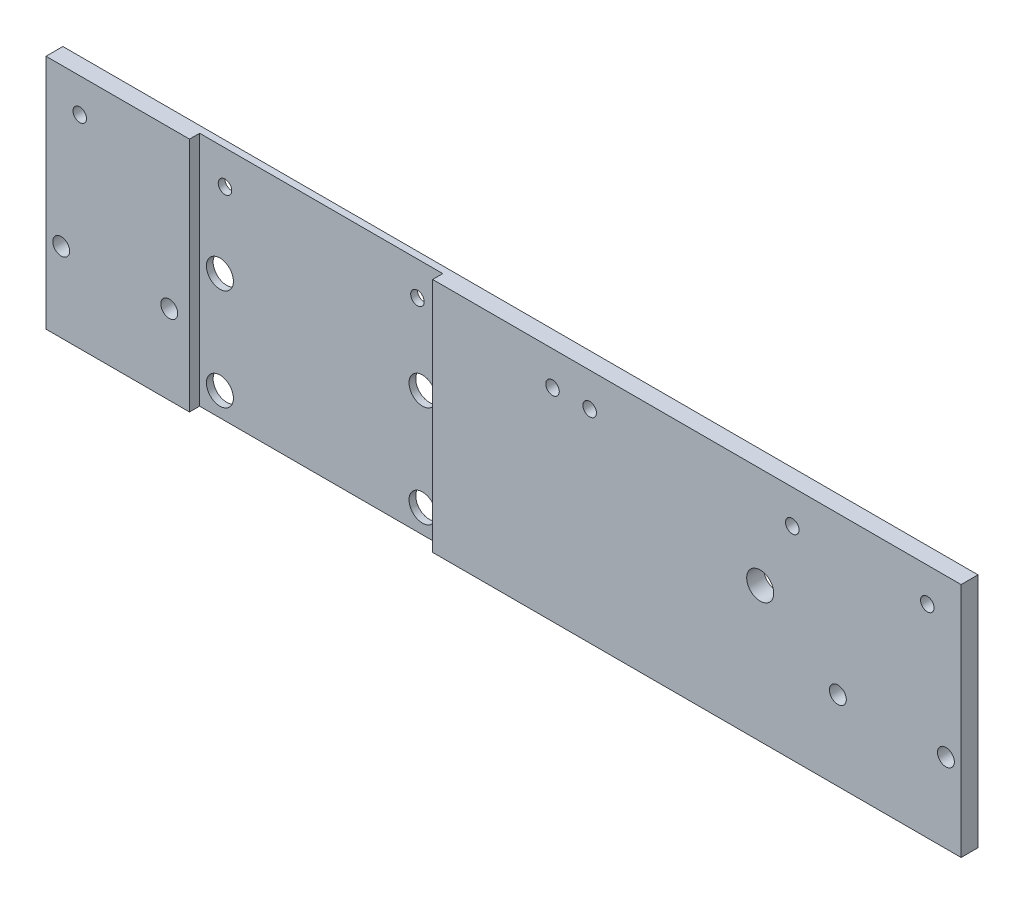
SolidWorks part; units mm, degrees
ref_plane "Ebene vorne" through (0, 0, 0) normal (0, 0, 1) x (1, 0, 0)
ref_plane "Ebene oben" through (0, 0, 0) normal (0, 1, 0) x (1, 0, 0)
ref_plane "Ebene rechts" through (0, 0, 0) normal (1, 0, 0) x (0, 0, -1)
sketch "Skizze1" plane through (0, 0, 0) normal (0, 0, 1) x (1, 0, 0)
  line L1 (0, 0) -> (271, 0)
  line L2 (0, 0) -> (0, 70)
  line L3 (0, 70) -> (271, 70)
  line L4 (271, 0) -> (271, 70)
  dimension "D1" = 271
  dimension "D2" = 70
extrude "Aufsatz-Linear austragen1" add sketch "Skizze1" along normal blind 5
sketch "Skizze2" plane through (0, 0, 5) normal (0, 0, 1) x (1, 0, 0)
  line L0 (271, 70) -> (0, 70) construction
  line L1 (42.5, 70) -> (114.5, 70)
  line L2 (42.5, 70) -> (42.5, 0)
  line L3 (42.5, 0) -> (114.5, 0)
  line L4 (114.5, 70) -> (114.5, 0)
  line L5 (0, 0) -> (271, 0) construction
  line L6 (0, 70) -> (0, 0) construction
  dimension "D1" = 72
  dimension "D2" = 42.5
extrude "Schnitt-Linear austragen1" cut sketch "Skizze2" against normal blind 3
sketch "Skizze3" plane through (0, 0, 0) normal (0, 0, -1) x (-1, 0, 0)
  line L1 (0, 70) -> (0, 0) construction
  line L3 (0, 0) -> (-271, 0) construction
  circle A0 centre (-48.5, 37) radius 4
  circle A1 centre (-108.5, 37) radius 4
  circle A2 centre (-108.5, 7) radius 4
  circle A3 centre (-48.5, 7) radius 4
  dimension "D1" = 8
  dimension "D2" = 30
  dimension "D3" = 48.5
  dimension "D4" = 60
  dimension "D5" = 7
extrude "Schnitt-Linear austragen2" cut sketch "Skizze3" against normal blind 10
sketch "Skizze4" plane through (0, 0, 0) normal (0, 0, -1) x (-1, 0, 0)
  line L3 (-271, 0) -> (-271, 70) construction
  line L4 (0, 0) -> (-271, 0) construction
  circle A0 centre (-234.5, 23.5) radius 2.5
  circle A1 centre (-266.5, 23.5) radius 2.5
  dimension "D1" = 5
  dimension "D2" = 4.5
  dimension "D3" = 23.5
  dimension "D4" = 32
extrude "Schnitt-Linear austragen3" cut sketch "Skizze4" against normal blind 10
sketch "Skizze5" plane through (0, 0, 0) normal (0, 0, -1) x (-1, 0, 0)
  line L0 (0, 0) -> (-271, 0) construction
  line L1 (0, 70) -> (0, 0) construction
  circle A0 centre (-36.5, 23.5) radius 2.5
  circle A1 centre (-4.5, 23.5) radius 2.5
  dimension "D4" = 5
  dimension "D1" = 23.5
  dimension "D2" = 4.5
  dimension "D3" = 32
extrude "Schnitt-Linear austragen4" cut sketch "Skizze5" against normal blind 10
sketch "Skizze6" plane through (0, 0, 0) normal (0, 0, -1) x (-1, 0, 0)
  line L0 (0, 70) -> (0, 0) construction
  line L1 (-114.5, 0) -> (-114.5, 70) construction
  line L2 (-271, 70) -> (0, 70) construction
  line L3 (-271, 0) -> (-271, 70) construction
  circle A0 centre (-10, 60) radius 2
  circle A1 centre (-50, 60) radius 2
  circle A2 centre (-161, 60) radius 2
  circle A3 centre (-221, 60) radius 2
  circle A4 centre (-261, 60) radius 2
  circle A5 centre (-107, 60) radius 2
  dimension "D1" = 4
  dimension "D2" = 10
  dimension "D3" = 10
  dimension "D4" = 50
  dimension "D5" = 10
  dimension "D6" = 50
  dimension "D7" = 110
  dimension "D8" = 7.5
extrude "Schnitt-Linear austragen5" cut sketch "Skizze6" against normal blind 10
sketch "Skizze7" plane through (0, 0, 0) normal (0, 0, -1) x (-1, 0, 0)
  line L0 (-271, 70) -> (0, 70) construction
  line L1 (-271, 0) -> (-271, 70) construction
  circle A0 centre (-211.5, 40) radius 4
  dimension "D3" = 8
  dimension "D1" = 30
  dimension "D2" = 59.5
extrude "Schnitt-Linear austragen6" cut sketch "Skizze7" against normal blind 10
sketch "Skizze8" plane through (0, 0, 0) normal (0, 0, -1) x (-1, 0, 0)
  line L0 (-271, 70) -> (0, 70) construction
  line L1 (0, 70) -> (0, 0) construction
  circle A0 centre (-150, 60) radius 2
  dimension "D3" = 4
  dimension "D1" = 10
  dimension "D2" = 150
extrude "Schnitt-Linear austragen7" cut sketch "Skizze8" against normal blind 10
